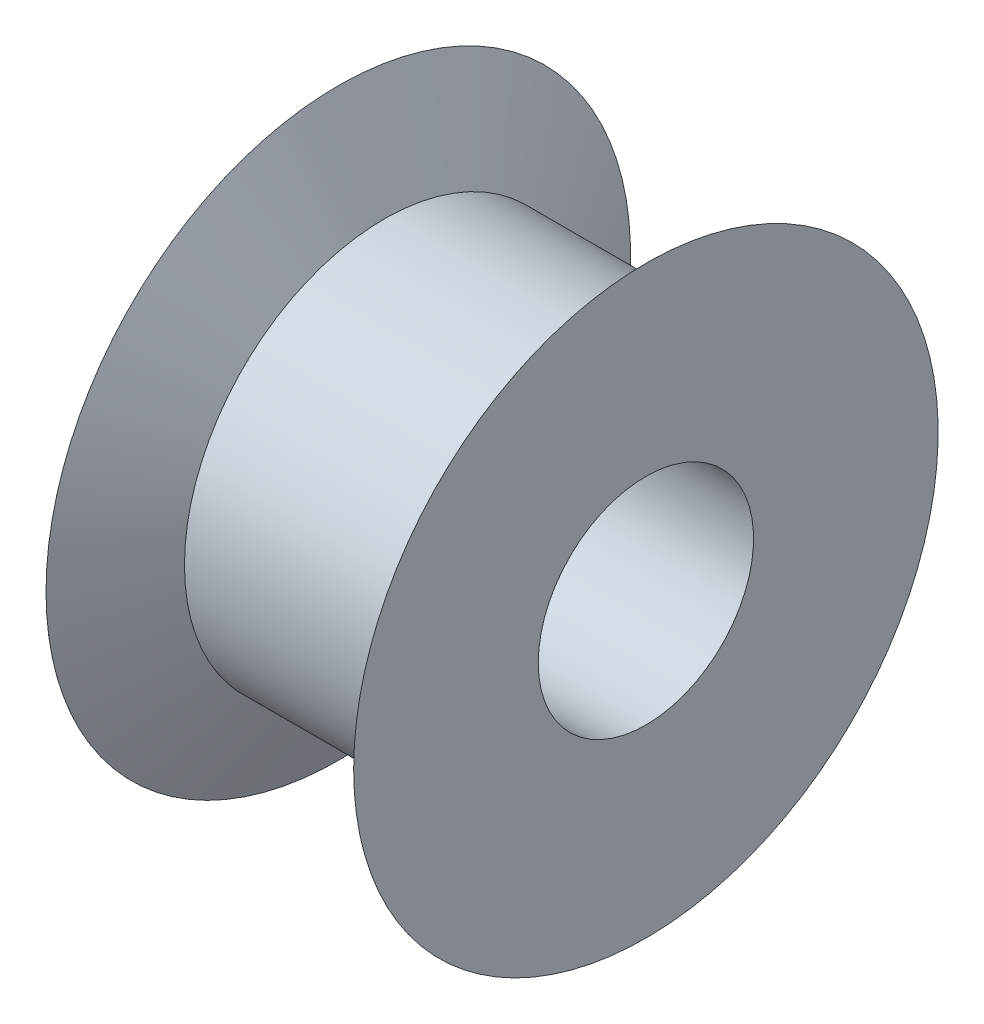
SolidWorks part; units mm, degrees
ref_plane "Front Plane" through (0, 0, 0) normal (0, 0, 1) x (1, 0, 0)
ref_plane "Top Plane" through (0, 0, 0) normal (0, 1, 0) x (1, 0, 0)
ref_plane "Right Plane" through (0, 0, 0) normal (1, 0, 0) x (0, 0, -1)
sketch "Sketch1" plane through (0, 0, 0) normal (0, 1, 0) x (1, 0, 0)
  line L0 (0, 0) -> (36.5834, 0) construction
  line L1 (21.7412, 3.5) -> (11.7412, 3.5)
  line L2 (11.7412, 3.5) -> (11.7412, 9.5)
  line L3 (11.7412, 9.5) -> (13.2412, 6.5)
  line L4 (13.2412, 6.5) -> (20.2412, 6.5)
  line L5 (20.2412, 6.5) -> (21.7412, 9.5)
  line L6 (21.7412, 9.5) -> (21.7412, 3.5)
  dimension "D1" = 6
  dimension "D2" = 7
  dimension "D3" = 1.5
  dimension "D4" = 10
  dimension "D5" = 6
  dimension "D6" = 3.5
revolve "Revolve1" add sketch "Sketch1" angle 360 about L0
